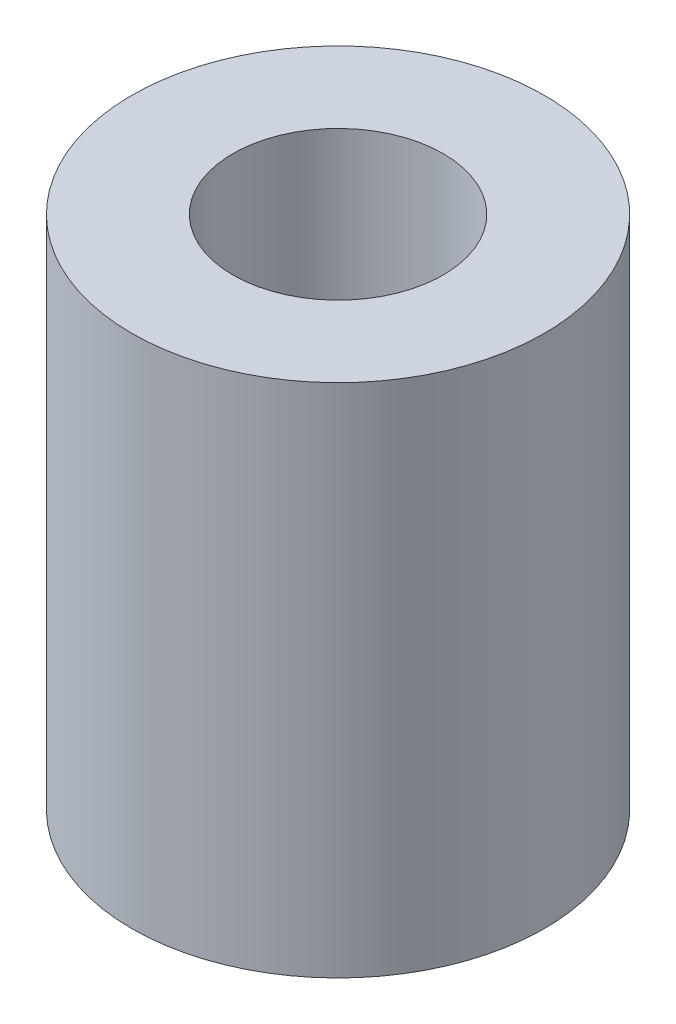
SolidWorks part; units mm, degrees
ref_plane "Ebene vorne" through (0, 0, 0) normal (0, 0, 1) x (1, 0, 0)
ref_plane "Ebene oben" through (0, 0, 0) normal (0, 1, 0) x (1, 0, 0)
ref_plane "Ebene rechts" through (0, 0, 0) normal (1, 0, 0) x (0, 0, -1)
sketch "Skizze1" plane through (0, 0, 0) normal (0, 1, 0) x (1, 0, 0)
  circle A0 centre (0, 0) radius 10
  dimension "D1" = 20
extrude "Zapfen" add sketch "Skizze1" along normal blind 25
hole_wizard "M12 Gewindebohrung1" positions "Skizze2" profile "Skizze3" tap size "M12" standard "DIN"
sketch "Skizze2" plane through (0, 25, 0) normal (0, 1, 0) x (1, 0, 0)
  point P0 (0, 0)
sketch "Skizze3" plane through (0, 25, 0) normal (1, 0, 0) x (0, 0, 1)
  line L0 (0, 0) -> (0, 23.0644)
  line L1 (0, 23.0644) -> (5.1, 20)
  line L2 (5.1, 20) -> (5.1, 0)
  line L5 (5.1, 0) -> (0, 0)
  line L10 (0, 23.0644) -> (-5.1, 20) construction
  line L11 (0, -6.35) -> (0, 107.95) construction
  dimension "Bohrerdurchmesser" = 10.2
  dimension "Bohrungstiefe" = 20
  dimension "Spitzenwinkel" = 118
cosmetic thread "Bohrungsgewinde1" parameters "D1"=18, "D2"=12
